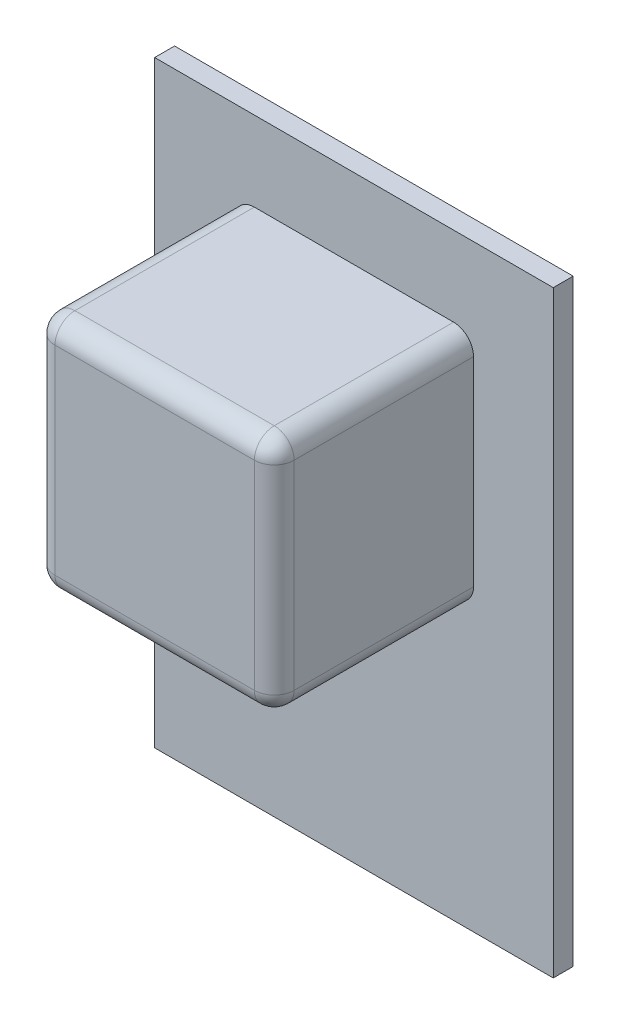
SolidWorks part; units mm, degrees
material "灰铸铁"
ref_plane "前视基准面" through (0, 0, 0) normal (0, 0, 1) x (1, 0, 0)
ref_plane "上视基准面" through (0, 0, 0) normal (0, 1, 0) x (1, 0, 0)
ref_plane "右视基准面" through (0, 0, 0) normal (1, 0, 0) x (0, 0, -1)
sketch "草图1" plane through (0, 0, 0) normal (0, 0, 1) x (1, 0, 0)
  line L1 (-100, -150) -> (100, -150)
  line L2 (-100, -150) -> (-100, 150)
  line L3 (-100, 150) -> (100, 150)
  line L4 (100, -150) -> (100, 150)
  line L5 (-100, -150) -> (100, 150) construction
  line L6 (-100, 150) -> (100, -150) construction
  point P0 (0, 0)
  dimension "D1" = 200
  dimension "D2" = 300
extrude "凸台-拉伸1" add sketch "草图1" against normal blind 10
sketch "草图2" plane through (0, 0, 0) normal (0, 0, 1) x (1, 0, 0)
  line L0 (100, 150) -> (-100, 150) construction
  line L1 (-60, -10) -> (60, -10)
  line L2 (-60, -10) -> (-60, 110)
  line L3 (-60, 110) -> (60, 110)
  line L4 (60, -10) -> (60, 110)
  line L5 (-60, -10) -> (60, 110) construction
  line L6 (-60, 110) -> (60, -10) construction
  point P0 (0, 50)
  dimension "D1" = 120
  dimension "D2" = 120
  dimension "D3" = 40
extrude "凸台-拉伸2" add sketch "草图2" along normal blind 100
fillet "圆角1" radius 10 8 edges at (0, -10, 100) (-60, 50, 100) (0, 110, 100) (60, 50, 100) (-60, -10, 50) (60, -10, 50) (60, 110, 50) (-60, 110, 50)
